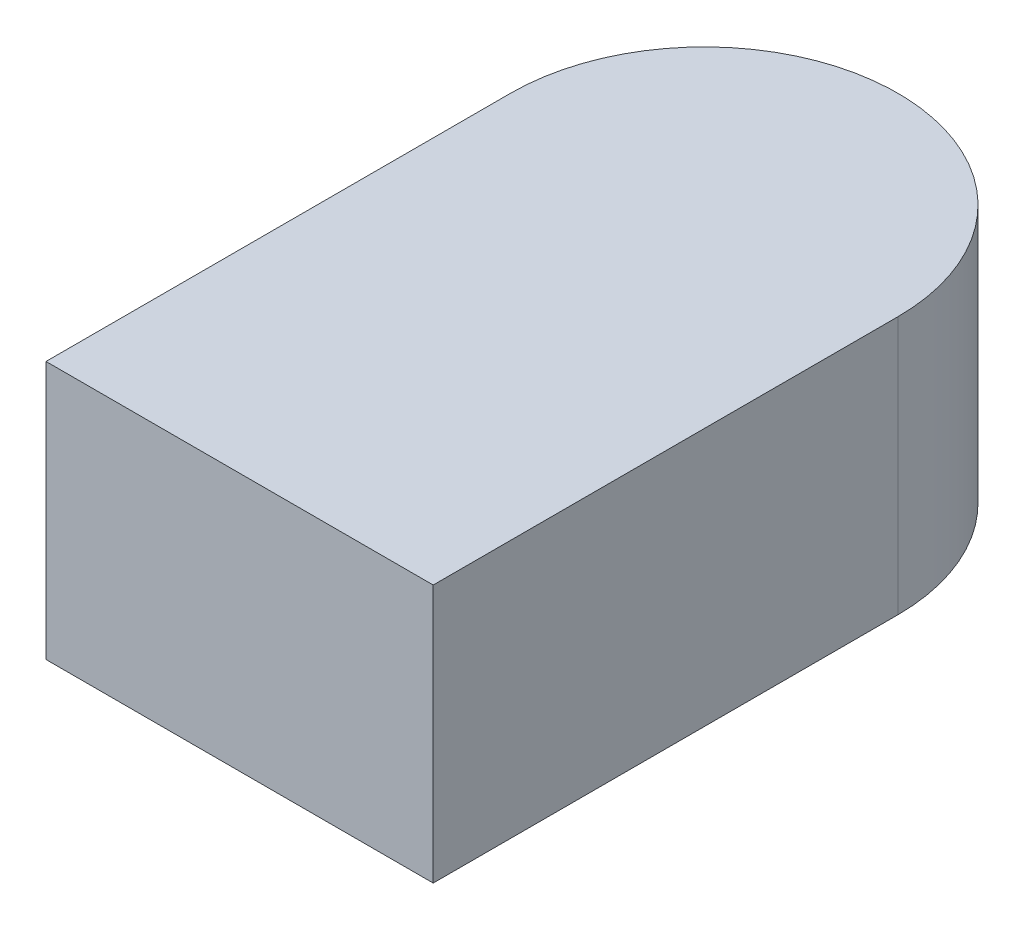
SolidWorks part; units mm, degrees
material "1060-H16"
ref_plane "Front Plane" through (0, 0, 0) normal (0, 0, 1) x (1, 0, 0)
ref_plane "Top Plane" through (0, 0, 0) normal (0, 1, 0) x (1, 0, 0)
ref_plane "Right Plane" through (0, 0, 0) normal (1, 0, 0) x (0, 0, -1)
sketch "Sketch1" plane through (0, 0, 0) normal (0, 1, 0) x (1, 0, 0)
  line L1 (-0.15, 0.18) -> (0.15, 0.18) construction
  line L2 (-0.15, 0.18) -> (-0.15, -0.18)
  line L3 (-0.15, -0.18) -> (0.15, -0.18)
  line L4 (0.15, 0.18) -> (0.15, -0.18)
  line L5 (-0.15, 0.18) -> (0.15, -0.18) construction
  line L6 (-0.15, -0.18) -> (0.15, 0.18) construction
  arc A1 (0.15, 0.18) -> (-0.15, 0.18) centre (0, 0.18) ccw
  point P0 (0, 0)
  point P7 (0, 0.33)
  dimension "D1" = 0.3
  dimension "D2" = 0.51
extrude "Boss-Extrude1" add sketch "Sketch1" along normal blind 0.2
